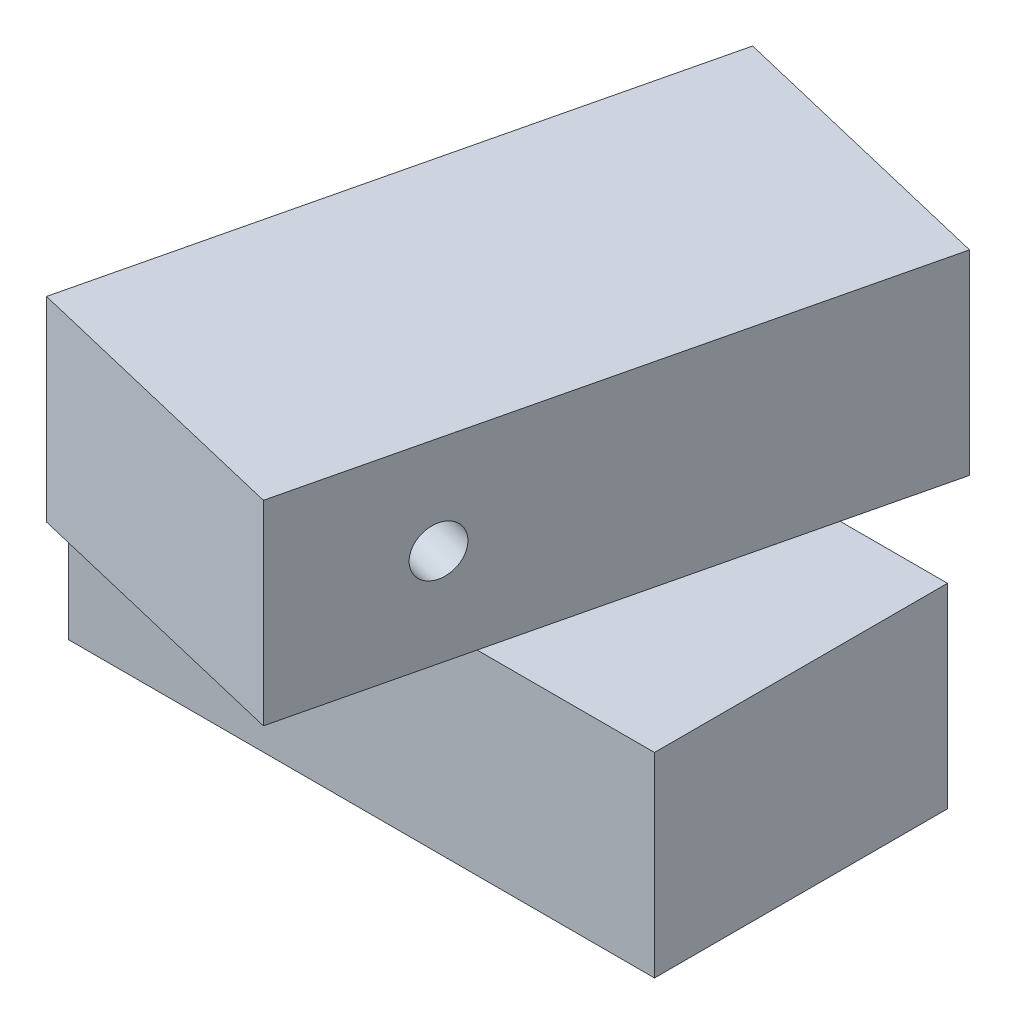
SolidWorks part; units mm, degrees
ref_plane "Front Plane" through (0, 0, 0) normal (0, 0, 1) x (1, 0, 0)
ref_plane "Top Plane" through (0, 0, 0) normal (0, 1, 0) x (1, 0, 0)
ref_plane "Right Plane" through (0, 0, 0) normal (1, 0, 0) x (0, 0, -1)
sketch "Sketch1" plane through (0, 0, 0) normal (0, 0, 1) x (1, 0, 0)
  line L1 (-60, -20) -> (60, -20)
  line L2 (-60, -20) -> (-60, 20)
  line L3 (-60, 20) -> (60, 20)
  line L4 (60, -20) -> (60, 20)
  line L5 (-60, -20) -> (60, 20) construction
  line L6 (-60, 20) -> (60, -20) construction
  point P0 (0, 0)
  dimension "D1" = 120
  dimension "D2" = 40
extrude "Boss-Extrude1" add sketch "Sketch1" along normal mid plane 60
sketch "Sketch2" plane through (0, 20, 0) normal (0, 1, 0) x (1, 0, 0)
  line L0 (-15.2386, 65.3283) -> (-43.1195, -51.3878)
  line L1 (-15.2386, 65.3283) -> (43.1195, 51.3878)
  line L2 (-43.1195, -51.3878) -> (15.2386, -65.3283)
  line L3 (43.1195, 51.3878) -> (15.2386, -65.3283)
  line L4 (43.1195, 51.3878) -> (-43.1195, -51.3878) construction
  line L5 (0, 74.6796) -> (0, -110.5554) construction
  line L6 (-79.0638, 0) -> (78.3076, 0) construction
  point P0 (0, 0)
  dimension "D1" = 120
  dimension "D2" = 60
  dimension "angle" = 40
extrude "Boss-Extrude2" add sketch "Sketch2" along normal blind 40
sketch "Sketch3" plane through (29.179, 50, 6.9702) normal (0.9726, 0, 0.2323) x (0.054, -0.9726, -0.226)
  line L0 (25.6385, -21.7918) -> (39.1975, 34.9693) construction
  line L2 (-23.6668, -56.0346) -> (15.2386, -65.3283) construction
  circle A0 centre (2.7007, -31.7345) radius 5
  point P2 (0, 0)
  dimension "D1" = 10
  dimension "D2" = 20
  dimension "D3" = 29.7614
extrude "Cut-Extrude1" cut sketch "Sketch3" against normal through all contours A0
equation "\"D2@Sketch1\"=\"D1@Sketch1\"/3"
equation "\"D1@Boss-Extrude1\"=\"D1@Sketch1\"/2"
equation "\"D2@Sketch2\"=\"D1@Sketch2\"/2"
equation "\"D1@Boss-Extrude2\"=\"D1@Sketch2\"/3"
equation "\"angle\"= 40"
equation "\"angle@Sketch2\"=\"angle\""
equation "\"Boss-Extrude2\" = 0"
